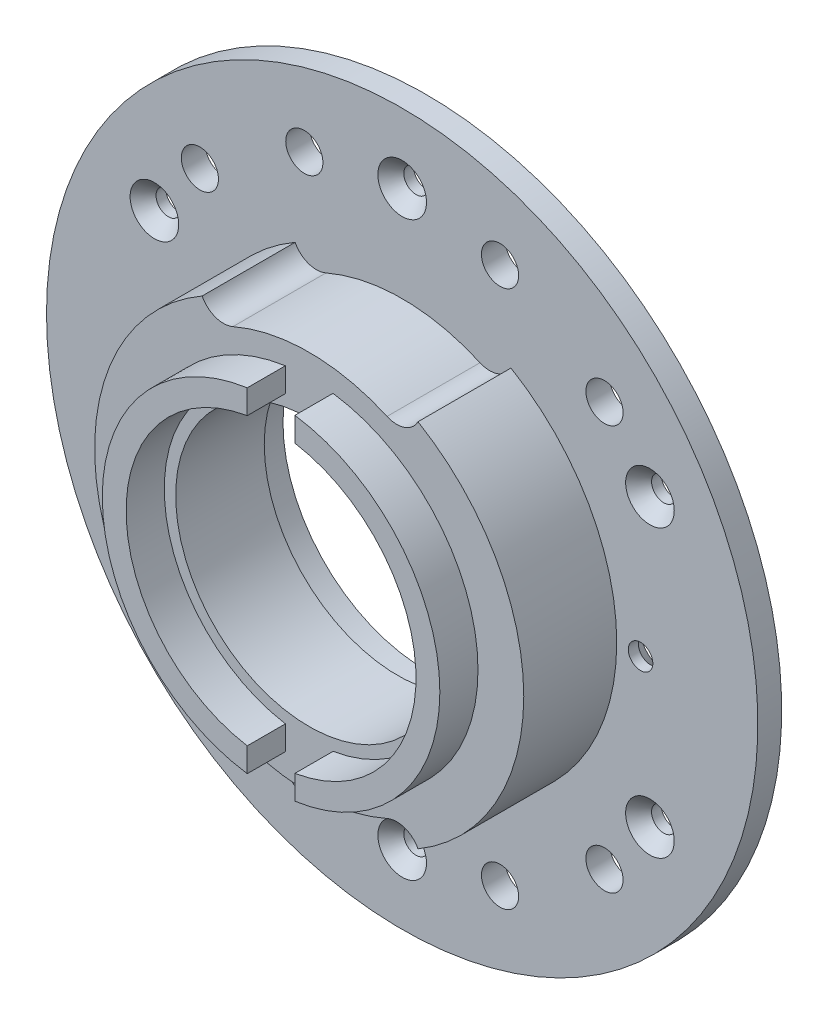
SolidWorks part; units mm, degrees
ref_plane "Front Plane" through (0, 0, 0) normal (0, 0, 1) x (1, 0, 0)
ref_plane "Top Plane" through (0, 0, 0) normal (0, 1, 0) x (1, 0, 0)
ref_plane "Right Plane" through (0, 0, 0) normal (1, 0, 0) x (0, 0, -1)
sketch "Sketch1" plane through (0, 0, 0) normal (0, 0, 1) x (1, 0, 0)
  circle A0 centre (0, 0) radius 28.575
  dimension "D1" = 57.15
extrude "Boss-Extrude1" add sketch "Sketch1" along normal blind 4.7625
sketch "Sketch2" plane through (0, 0, 4.7625) normal (0, 0, 1) x (1, 0, 0)
  circle A0 centre (0, 0) radius 17.78
  dimension "D1" = 35.56
extrude "Cut-Extrude1" cut sketch "Sketch2" against normal through all
sketch "Sketch3" plane through (0, 0, 0) normal (0, 0, -1) x (-1, 0, 0)
  circle A0 centre (0, 0) radius 26.035
  dimension "D1" = 52.07
extrude "Cut-Extrude2" [suppressed] cut sketch "Sketch3" against normal blind 1.905
sketch "Sketch9" plane through (0, 0, 0) normal (0, 0, -1) x (-1, 0, 0)
  circle A0 centre (0, 0) radius 28.575
  circle A1 centre (0, 0) radius 17.78
  dimension "D1" = 35.56
extrude "Boss-Extrude4" add sketch "Sketch9" along normal blind 7.62
sketch "Sketch4" plane through (0, 0, 4.7625) normal (0, 0, 1) x (1, 0, 0)
  circle A0 centre (0, 0) radius 19.304
  circle A1 centre (0, 0) radius 22.479
  dimension "D1" = 38.608
  dimension "D2" = 3.175
extrude "Boss-Extrude2" add sketch "Sketch4" along normal blind 5.08
sketch "Sketch5" plane through (0, 0, 9.8425) normal (0, 0, 1) x (1, 0, 0)
  line L0 (0, -2.6194) -> (0, 2.6194) construction
  line L1 (-3.175, 25.4) -> (3.175, 25.4)
  line L2 (-3.175, 25.4) -> (-3.175, -25.4)
  line L3 (-3.175, -25.4) -> (3.175, -25.4)
  line L4 (3.175, 25.4) -> (3.175, -25.4)
  dimension "D1" = 3.175
  dimension "D2" = 6.35
  dimension "D3" = 50.8
  dimension "D4" = 25.4
extrude "Cut-Extrude3" cut sketch "Sketch5" against normal up to surface (5.08 mm away) up to face at (28.575, 0, 4.7625)
sketch "Sketch7" plane through (0, 0, 4.7625) normal (0, 0, 1) x (1, 0, 0)
  arc A0 (-11.4206, 26.1935) -> (11.664, 26.086) centre (0, 0) cw construction
  circle A1 centre (0, 0) radius 28.575 construction
  arc A2 (12.96, 28.9845) -> (-12.6896, 29.1039) centre (0, 0) ccw
  arc A3 (10.368, 23.1876) -> (-10.1516, 23.2831) centre (0, 0) ccw
  arc A4 (10.368, 23.1876) -> (12.96, 28.9845) centre (11.664, 26.086) ccw
  arc A5 (-12.6896, 29.1039) -> (-10.1516, 23.2831) centre (-11.4206, 26.1935) ccw
  point P6 (0.133, 28.5747)
  dimension "D1" = 3.175
extrude "Cut-Extrude4" cut sketch "Sketch7" against normal through all
mirror "Mirror1" about plane through (0, 0, 0) normal (0, 1, 0) of "Cut-Extrude4"
sketch "Sketch10" plane through (0, 0, -7.62) normal (0, 0, -1) x (-1, 0, 0)
  circle A0 centre (0, 0) radius 19.05
  dimension "D1" = 38.1
extrude "Cut-Extrude5" cut sketch "Sketch10" against normal blind 0.5918
sketch "Sketch11" plane through (0, 0, -7.62) normal (0, 0, -1) x (-1, 0, 0)
  circle A0 centre (0, 0) radius 47.371
  circle A1 centre (0, 0) radius 19.05
  dimension "D1" = 94.742
  dimension "D2" = 38.1
extrude "Boss-Extrude5" add sketch "Sketch11" along normal blind 3.175
hole_wizard "CSK for #4 Flat Head Socket Cap Screw1" positions "Sketch13" profile "Sketch12" countersink size "#4" standard "ANSI Inch"
sketch "Sketch13" plane through (0, 0, -10.795) normal (0, 0, -1) x (-1, 0, 0)
  point P0 (31.75, 0)
  dimension "D1" = 31.75
sketch "Sketch12" plane through (-31.75, 0, -10.795) normal (1, 0, 0) x (0, 1, 0)
  line L0 (0, 0) -> (0, 6.0606)
  line L1 (0, 6.0606) -> (1.6319, 5.08)
  line L2 (1.6319, 5.08) -> (1.6319, 1.8481)
  line L3 (1.6319, 1.8481) -> (3.2385, 0)
  line L5 (3.2385, 0) -> (0, 0)
  line L6 (-1.632, 1.8481) -> (-3.2385, 0) construction
  line L10 (0, 6.0606) -> (-1.6319, 5.08) construction
  line L11 (0, -6.35) -> (0, 107.95) construction
  dimension "Hole Dia." = 3.2639
  dimension "Hole Depth" = 5.08
  dimension "Near C'Sink Dia." = 6.477
  dimension "Near C'Sink Angle" = 82
  dimension "Drill Angle" = 118
mirror "Mirror2" about plane through (0, 0, 0) normal (1, 0, 0) of "CSK for #4 Flat Head Socket Cap Screw1"
hole_wizard "CSK for #4 Flat Head Socket Cap Screw3" positions "Sketch17" profile "Sketch16" countersink size "#4" standard "ANSI Inch"
sketch "Sketch17" plane through (0, 0, -7.62) normal (0, 0, 1) x (1, 0, 0)
  point P0 (0, 38.1)
  dimension "D1" = 38.1
sketch "Sketch16" plane through (0, 38.1, -7.62) normal (1, 0, 0) x (0, -1, 0)
  line L0 (0, 0) -> (0, 4.1556)
  line L1 (0, 4.1556) -> (1.6319, 3.175)
  line L2 (1.6319, 3.175) -> (1.6319, 1.8481)
  line L3 (1.6319, 1.8481) -> (3.2385, 0)
  line L5 (3.2385, 0) -> (0, 0)
  line L6 (-1.6319, 1.8481) -> (-3.2385, 0) construction
  line L10 (0, 4.1556) -> (-1.6319, 3.175) construction
  line L11 (0, -6.35) -> (0, 107.95) construction
  dimension "Hole Dia." = 3.2639
  dimension "Hole Depth" = 3.175
  dimension "Near C'Sink Dia." = 6.477
  dimension "Near C'Sink Angle" = 82
  dimension "Drill Angle" = 118
pattern_circular "CirPattern1" count 6 over 360 about axis through (0, 0, 0) along (0, 0, 1) of "CSK for #4 Flat Head Socket Cap Screw3"
sketch "Sketch19" plane through (0, 0, -10.795) normal (0, 0, -1) x (-1, 0, 0)
  line L1 (13.031, 35.8023) -> (0, 0) construction
  line L2 (0, 0) -> (53, 0) construction
  line L3 (11.3506, 0) -> (-11.3506, 0) construction
  circle A0 centre (13.031, 35.8023) radius 2.4765
  dimension "D1" = 4.953
  dimension "D3" = 70
  dimension "D2" = 38.1
extrude "Cut-Extrude7" cut sketch "Sketch19" against normal through all
pattern_circular "CirPattern2" count 2 every 25 about axis through (0, 0, -10.795) along (0, 0, -1) of "Cut-Extrude7"
mirror "Mirror3" about plane through (0, 0, 0) normal (1, 0, 0) of "CirPattern2", "Cut-Extrude7"
mirror "Mirror4" about plane through (0, 0, 0) normal (0, 1, 0) of "Mirror3", "CirPattern2", "Cut-Extrude7"
equation "\"D1@Sketch5\"=\"D2@Sketch5\"/2"
